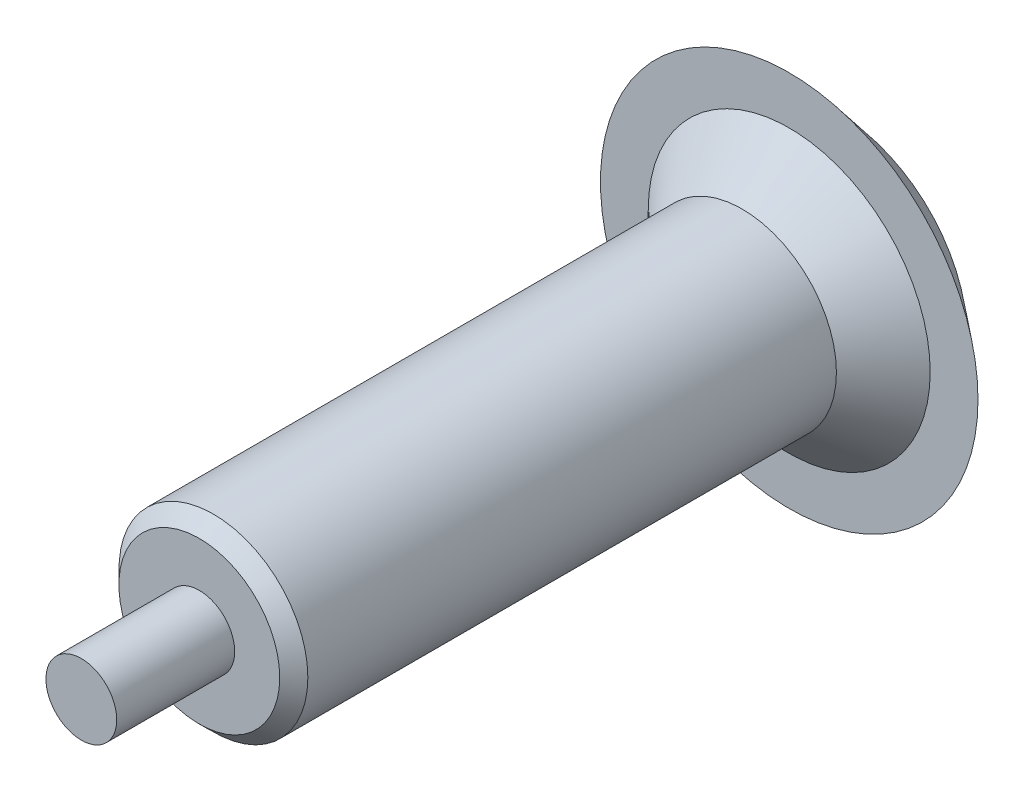
SolidWorks part; units mm, degrees
ref_plane "Front Plane" through (0, 0, 0) normal (0, 0, 1) x (1, 0, 0)
ref_plane "Top Plane" through (0, 0, 0) normal (0, 1, 0) x (1, 0, 0)
ref_plane "Right Plane" through (0, 0, 0) normal (1, 0, 0) x (0, 0, -1)
sketch "Sketch1" plane through (0, 0, 0) normal (0, 1, 0) x (1, 0, 0)
  line L0 (0, 0) -> (0, 117.2416) construction
  line L1 (0, 163.9099) -> (27.7865, 163.9099)
  line L2 (27.7865, 163.9099) -> (40, 153.9099)
  line L3 (40, 153.9099) -> (29.8695, 153.9099)
  line L5 (29.8695, 153.9099) -> (20, 143.9099)
  line L6 (20, 143.9099) -> (20, 31.9099)
  line L7 (20, 31.9099) -> (17.0392, 28.9099)
  line L8 (17.0392, 28.9099) -> (7.5, 28.9099)
  line L9 (7.5, 28.9099) -> (7.5, 3.9099)
  line L10 (7.5, 3.9099) -> (0, 3.9099)
  line L11 (0, 3.9099) -> (0, 163.9099)
  dimension "D1" = 80
  dimension "D2" = 160
  dimension "D3" = 3
  dimension "D4" = 10
  dimension "D5" = 150
  dimension "D6" = 40
  dimension "D7" = 15
  dimension "D8" = 25
revolve "Revolve1" add sketch "Sketch1" angle 360 about L0
